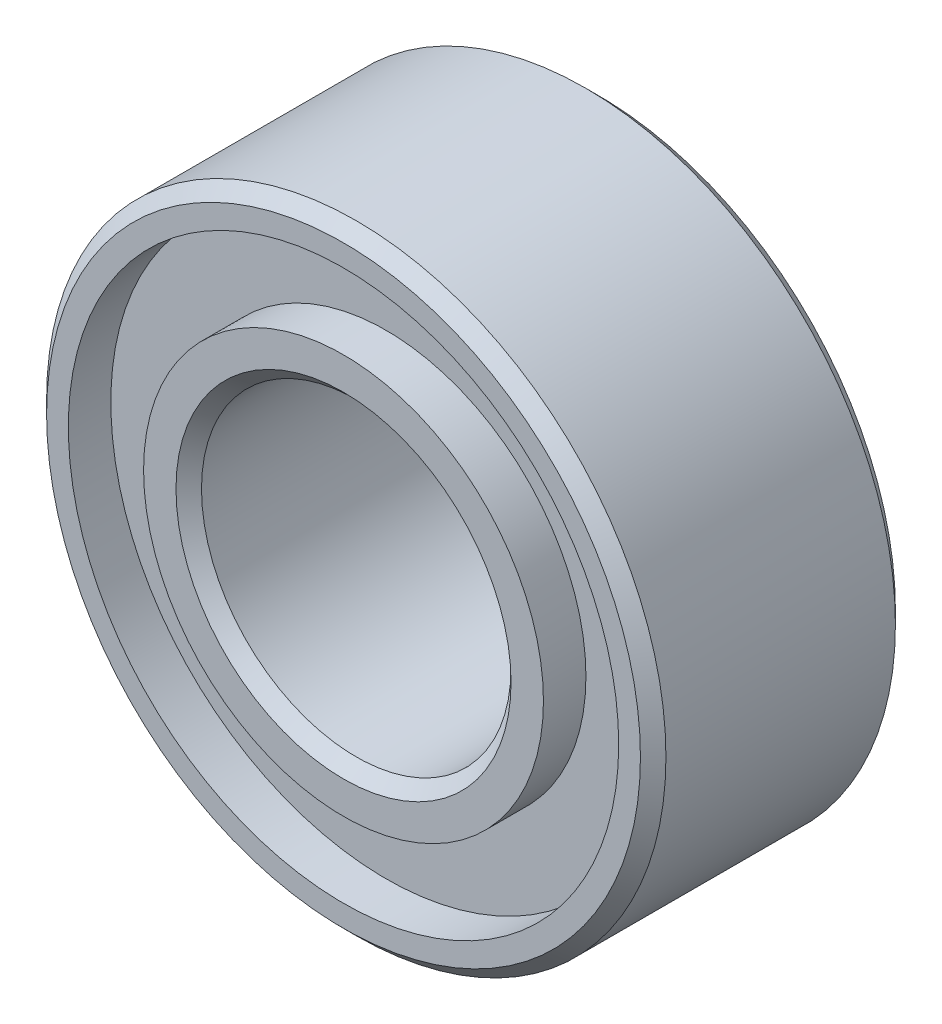
SolidWorks part; units mm, degrees
material "Alloy Steel"
ref_plane "Front Plane" through (0, 0, 0) normal (0, 0, 1) x (1, 0, 0)
ref_plane "Top Plane" through (0, 0, 0) normal (0, 1, 0) x (1, 0, 0)
ref_plane "Right Plane" through (0, 0, 0) normal (1, 0, 0) x (0, 0, -1)
ref_plane "Plane1" through (0, 0, 4.94) normal (0, 0, 1) x (1, 0, 0)
sketch "Sketch1" plane through (0, 0, 4.94) normal (0, 0, 1) x (1, 0, 0)
  circle A0 centre (0, 0) radius 6
  dimension "D1" = 12
extrude "Extrude1" add sketch "Sketch1" against normal blind 4.94
hole_wizard "Hole1" positions "Sketch3" profile "Sketch2" legacy
sketch "Sketch3" plane through (0, 0, 4.94) normal (0, 0, 1) x (1, 0, 0)
  point P0 (0, 0)
sketch "Sketch2" plane through (0, 0, 4.94) normal (1, 0, 0) x (0, -1, 0)
  line L0 (0, 0) -> (0, 0.8233)
  line L1 (0, 0.8233) -> (5.3318, 0.8233)
  line L2 (5.3318, 0.8233) -> (5.3318, 0)
  line L3 (5.3318, 0) -> (0, 0)
  line L4 (0, 110) -> (0, -10) construction
  dimension "Diameter" = 10.6635
  dimension "Depth" = 0.8233
sketch "Sketch4" plane through (0, 0, 4.1167) normal (0, 0, 1) x (1, 0, 0)
  circle A0 centre (0, 0) radius 3.8736
  dimension "D1" = 7.7473
extrude "Extrude2" add sketch "Sketch4" along normal blind 0.8233
hole_wizard "Hole2" positions "Sketch6" profile "Sketch5" legacy
sketch "Sketch6" plane through (0, 0, 0) normal (0, 0, -1) x (-1, 0, 0)
  point P0 (0, 0)
sketch "Sketch5" plane through (0, 0, 0) normal (1, 0, 0) x (0, 1, 0)
  line L0 (0, 0) -> (0, 0.8233)
  line L1 (0, 0.8233) -> (5.3318, 0.8233)
  line L2 (5.3318, 0.8233) -> (5.3318, 0)
  line L3 (5.3318, 0) -> (0, 0)
  line L4 (0, 110) -> (0, -10) construction
  dimension "Diameter" = 10.6635
  dimension "Depth" = 0.8233
sketch "Sketch7" plane through (0, 0, 0.8233) normal (0, 0, -1) x (-1, 0, 0)
  circle A0 centre (0, 0) radius 3.8736
  dimension "D1" = 7.7473
extrude "Extrude3" add sketch "Sketch7" along normal blind 0.8233
hole_wizard "Hole3" positions "Sketch9" profile "Sketch8" legacy
sketch "Sketch9" plane through (0, 0, 0) normal (0, 0, -1) x (-1, 0, 0)
  point P0 (0, 0)
sketch "Sketch8" plane through (0, 0, 0) normal (1, 0, 0) x (0, 1, 0)
  line L0 (0, 0) -> (0, 4.94)
  line L1 (0, 4.94) -> (2.9988, 4.94)
  line L2 (2.9988, 4.94) -> (2.9988, 0)
  line L3 (2.9988, 0) -> (0, 0)
  line L4 (0, 110) -> (0, -10) construction
  dimension "Diameter" = 5.9975
  dimension "Depth" = 4.94
chamfer "Chamfer1" distance 0.247 angle 45 4 edges at (-2.9988, 0, 0) (-6, 0, 0) (-6, 0, 4.94) (2.9988, 0, 4.94)
